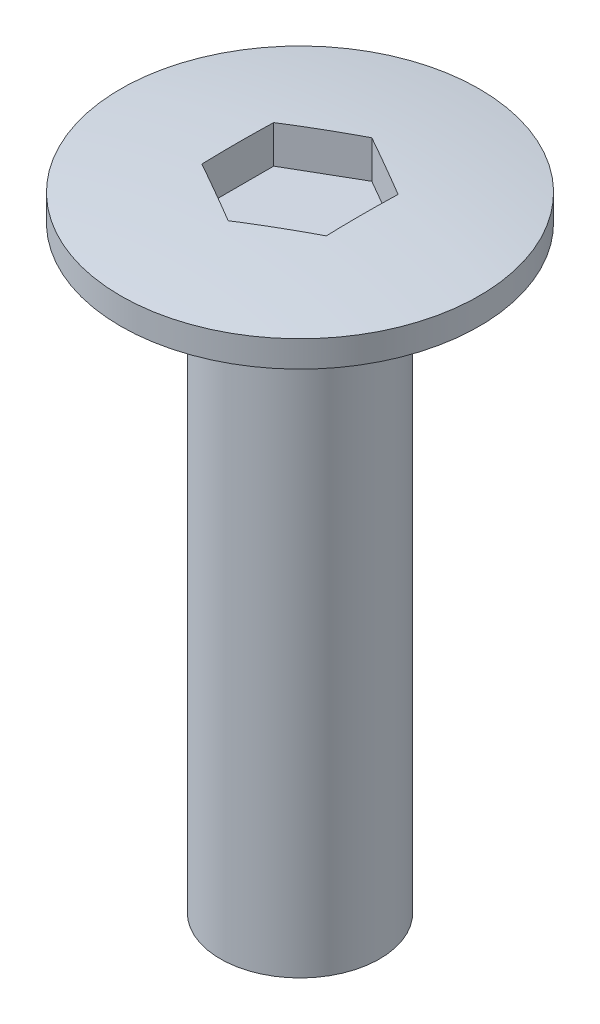
SolidWorks part; units mm, degrees
ref_plane "前视基准面" through (0, 0, 0) normal (0, 0, 1) x (1, 0, 0)
ref_plane "上视基准面" through (0, 0, 0) normal (0, 1, 0) x (1, 0, 0)
ref_plane "右视基准面" through (0, 0, 0) normal (1, 0, 0) x (0, 0, -1)
sketch "草图1" plane through (0, 0, 0) normal (0, 1, 0) x (1, 0, 0)
  circle A0 centre (0, 0) radius 4.5
  dimension "D1" = 9
extrude "凸台-拉伸1" add sketch "草图1" along normal blind 1
sketch "草图2" plane through (0, 0, 0) normal (0, -1, 0) x (1, 0, 0)
  circle A0 centre (0, 0) radius 2
  dimension "D1" = 4
extrude "凸台-拉伸2" add sketch "草图2" along normal blind 15
sketch "草图3" plane through (0, 0, 0) normal (0, 0, 1) x (1, 0, 0)
  line L0 (4.5, 1) -> (-4.5, 1) construction
  line L1 (5.5901, 0.4746) -> (5.7344, 3.2793)
  line L3 (0, 1) -> (0, 3.3294)
  line L6 (0, 0) -> (0, 0.5088)
  line L7 (0, 3.3294) -> (5.7344, 3.2793)
  arc A0 (5.5901, 0.4746) -> (0, 1) centre (0, -29) ccw
  dimension "D1" = 60
revolve "切除-旋转2" cut sketch "草图3" angle 360 about L6
sketch "草图4" plane through (0, 0, 0) normal (0, -1, 0) x (1, 0, 0)
  line L1 (0, -1.8024) -> (1.5609, -0.9012)
  line L2 (1.5609, -0.9012) -> (1.5609, 0.9012)
  line L3 (1.5609, 0.9012) -> (0, 1.8024)
  line L4 (0, 1.8024) -> (-1.5609, 0.9012)
  line L5 (-1.5609, 0.9012) -> (-1.5609, -0.9012)
  line L6 (-1.5609, -0.9012) -> (0, -1.8024)
  circle A0 centre (0, 0) radius 1.5609 construction
extrude "切除-拉伸1" cut sketch "草图4" against normal blind 1
